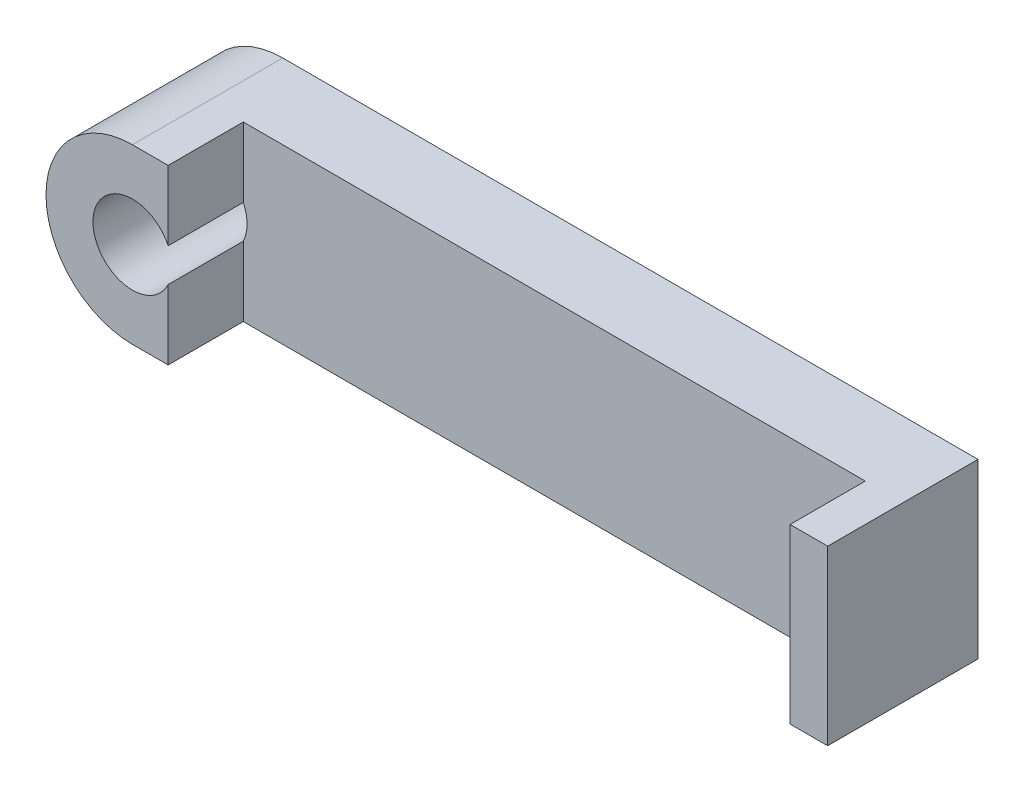
SolidWorks part; units mm, degrees
ref_plane "Front Plane" through (0, 0, 0) normal (0, 0, 1) x (1, 0, 0)
ref_plane "Top Plane" through (0, 0, 0) normal (0, 1, 0) x (1, 0, 0)
ref_plane "Right Plane" through (0, 0, 0) normal (1, 0, 0) x (0, 0, -1)
sketch "Sketch1" plane through (0, 0, 0) normal (0, 0, 1) x (1, 0, 0)
  line L0 (0, 0) -> (62.29, 0) construction
  line L1 (0, 4.6) -> (62.29, 4.6)
  line L2 (0, -4.6) -> (62.29, -4.6)
  circle A0 centre (0, 0) radius 2.1
  circle A1 centre (62.29, 0) radius 2.1
  arc A2 (0, 4.6) -> (0, -4.6) centre (0, 0) ccw
  arc A3 (62.29, -4.6) -> (62.29, 4.6) centre (62.29, 0) ccw
  point P5 (31.145, 0)
  dimension "D1" = 4.2
  dimension "D2" = 2.5
  dimension "D3" = 62.29
extrude "Boss-Extrude1" [suppressed] add sketch "Sketch1" along normal blind 4
sketch "Sketch2" plane through (0, 0, 0) normal (0, 0, 1) x (1, 0, 0)
  line L0 (0, 4.6) -> (37, 4.6)
  line L1 (37, 4.6) -> (37, -4.6)
  line L2 (37, -4.6) -> (0, -4.6)
  circle A6 centre (0, 0) radius 2.1
  arc A7 (0, 4.6) -> (0, -4.6) centre (0, 0) ccw
  point P3 (0, 0)
  dimension "D2" = 2.5
  dimension "D3" = 37
  dimension "D1" = 4.2
extrude "Boss-Extrude2" add sketch "Sketch2" along normal blind 4
sketch "Sketch3" plane through (0, 0, 4) normal (0, 0, 1) x (1, 0, 0)
  line L0 (0, -4.6) -> (37, -4.6) construction
  line L1 (37, 4.6) -> (35, 4.6)
  line L2 (37, 4.6) -> (37, -4.6)
  line L3 (37, -4.6) -> (35, -4.6)
  line L4 (35, 4.6) -> (35, -4.6)
  line L5 (1.9, 4.6) -> (1.9, 0.8944)
  line L6 (0, 4.6) -> (1.9, 4.6)
  line L7 (37, 4.6) -> (0, 4.6) construction
  line L8 (0, -4.6) -> (1.9, -4.6)
  line L9 (1.9, -0.8944) -> (1.9, -4.6)
  arc A0 (1.9, 0.8944) -> (1.9, -0.8944) centre (0, 0) ccw
  arc A1 (0, 4.6) -> (0, -4.6) centre (0, 0) ccw
  circle A2 centre (0, 0) radius 2.1 construction
  arc A3 (0, 4.6) -> (0, -4.6) centre (0, 0) ccw construction
  point P23 (0, 0)
  point P24 (0, 0)
  dimension "D2" = 0.2
  dimension "D1" = 2
extrude "Boss-Extrude3" add sketch "Sketch3" along normal blind 4
